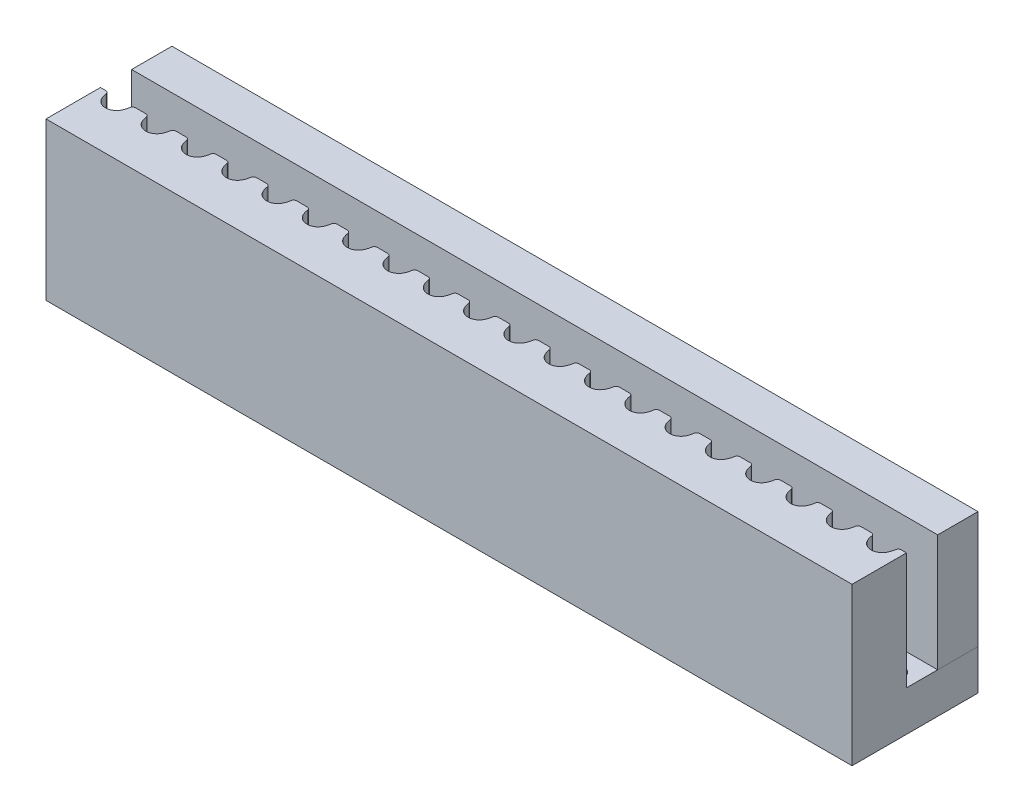
SolidWorks part; units mm, degrees
ref_plane "Front Plane" through (0, 0, 0) normal (0, 0, 1) x (1, 0, 0)
ref_plane "Top Plane" through (0, 0, 0) normal (0, 1, 0) x (1, 0, 0)
ref_plane "Right Plane" through (0, 0, 0) normal (1, 0, 0) x (0, 0, -1)
sketch "Sketch1" plane through (0, 0, 0) normal (0, 1, 0) x (1, 0, 0)
  line L0 (-20, 0.95) -> (20, 0.95) construction
  line L1 (0, -55) -> (0, 55) construction
  line L2 (-55, 0) -> (55, 0) construction
  line L3 (-20, 0.32) -> (20, 0.32)
  line L4 (-20, -0.43) -> (20, -0.43) construction
  line L5 (-19, 1.863) -> (-19, -1.7327) construction
  line L6 (-18.6, 1.863) -> (-18.6, -1.7327) construction
  line L7 (-20.453, 0.574) -> (20.5239, 0.574) construction
  line L8 (-19.4, 1.863) -> (-19.4, -1.7327) construction
  line L11 (-19.5915, 0.1896) -> (-17.5915, 0.1896) construction
  line L12 (20, 0.32) -> (20, -2.38)
  line L13 (20, -2.38) -> (-20, -2.38)
  line L14 (-20, -2.38) -> (-20, 0.32)
  line L17 (20, 1.87) -> (-20, 1.87)
  line L18 (20, 1.87) -> (20, 3.87)
  line L19 (20, 3.87) -> (-20, 3.87)
  line L20 (-20, 1.87) -> (-20, 3.87)
  circle A0 centre (-19, 0.125) radius 0.555
  arc A3 (-19.5915, 0.1896) -> (-19.7402, 0.32) centre (-19.7402, 0.17) ccw
  arc A4 (-18.2598, 0.32) -> (-18.4085, 0.1896) centre (-18.2598, 0.17) ccw
  arc A5 (-19.5915, 0.1896) -> (-19.4989, -0.1182) centre (-18.6, 0.32) ccw
  arc A6 (-18.5011, -0.1182) -> (-18.4085, 0.1896) centre (-19.4, 0.32) ccw
  arc A7 (-17.5915, 0.1896) -> (-17.7402, 0.32) centre (-17.7402, 0.17) ccw
  arc A8 (-17.5915, 0.1896) -> (-17.4989, -0.1182) centre (-16.6, 0.32) ccw
  circle A9 centre (-17, 0.125) radius 0.555
  arc A10 (-16.2598, 0.32) -> (-16.4085, 0.1896) centre (-16.2598, 0.17) ccw
  arc A11 (-16.5011, -0.1182) -> (-16.4085, 0.1896) centre (-17.4, 0.32) ccw
  arc A12 (-15.5915, 0.1896) -> (-15.7402, 0.32) centre (-15.7402, 0.17) ccw
  arc A13 (-15.5915, 0.1896) -> (-15.4989, -0.1182) centre (-14.6, 0.32) ccw
  circle A14 centre (-15, 0.125) radius 0.555
  arc A15 (-14.2598, 0.32) -> (-14.4085, 0.1896) centre (-14.2598, 0.17) ccw
  arc A16 (-14.5011, -0.1182) -> (-14.4085, 0.1896) centre (-15.4, 0.32) ccw
  arc A17 (-13.5915, 0.1896) -> (-13.7402, 0.32) centre (-13.7402, 0.17) ccw
  arc A18 (-13.5915, 0.1896) -> (-13.4989, -0.1182) centre (-12.6, 0.32) ccw
  circle A19 centre (-13, 0.125) radius 0.555
  arc A20 (-12.2598, 0.32) -> (-12.4085, 0.1896) centre (-12.2598, 0.17) ccw
  arc A21 (-12.5011, -0.1182) -> (-12.4085, 0.1896) centre (-13.4, 0.32) ccw
  arc A22 (-11.5915, 0.1896) -> (-11.7402, 0.32) centre (-11.7402, 0.17) ccw
  arc A23 (-11.5915, 0.1896) -> (-11.4989, -0.1182) centre (-10.6, 0.32) ccw
  circle A24 centre (-11, 0.125) radius 0.555
  arc A25 (-10.2598, 0.32) -> (-10.4085, 0.1896) centre (-10.2598, 0.17) ccw
  arc A26 (-10.5011, -0.1182) -> (-10.4085, 0.1896) centre (-11.4, 0.32) ccw
  arc A27 (-9.5915, 0.1896) -> (-9.7402, 0.32) centre (-9.7402, 0.17) ccw
  arc A28 (-9.5915, 0.1896) -> (-9.4989, -0.1182) centre (-8.6, 0.32) ccw
  circle A29 centre (-9, 0.125) radius 0.555
  arc A30 (-8.2598, 0.32) -> (-8.4085, 0.1896) centre (-8.2598, 0.17) ccw
  arc A31 (-8.5011, -0.1182) -> (-8.4085, 0.1896) centre (-9.4, 0.32) ccw
  arc A32 (-7.5915, 0.1896) -> (-7.7402, 0.32) centre (-7.7402, 0.17) ccw
  arc A33 (-7.5915, 0.1896) -> (-7.4989, -0.1182) centre (-6.6, 0.32) ccw
  circle A34 centre (-7, 0.125) radius 0.555
  arc A35 (-6.2598, 0.32) -> (-6.4085, 0.1896) centre (-6.2598, 0.17) ccw
  arc A36 (-6.5011, -0.1182) -> (-6.4085, 0.1896) centre (-7.4, 0.32) ccw
  arc A37 (-5.5915, 0.1896) -> (-5.7402, 0.32) centre (-5.7402, 0.17) ccw
  arc A38 (-5.5915, 0.1896) -> (-5.4989, -0.1182) centre (-4.6, 0.32) ccw
  circle A39 centre (-5, 0.125) radius 0.555
  arc A40 (-4.2598, 0.32) -> (-4.4085, 0.1896) centre (-4.2598, 0.17) ccw
  arc A41 (-4.5011, -0.1182) -> (-4.4085, 0.1896) centre (-5.4, 0.32) ccw
  arc A42 (-3.5915, 0.1896) -> (-3.7402, 0.32) centre (-3.7402, 0.17) ccw
  arc A43 (-3.5915, 0.1896) -> (-3.4989, -0.1182) centre (-2.6, 0.32) ccw
  circle A44 centre (-3, 0.125) radius 0.555
  arc A45 (-2.2598, 0.32) -> (-2.4085, 0.1896) centre (-2.2598, 0.17) ccw
  arc A46 (-2.5011, -0.1182) -> (-2.4085, 0.1896) centre (-3.4, 0.32) ccw
  arc A47 (-1.5915, 0.1896) -> (-1.7402, 0.32) centre (-1.7402, 0.17) ccw
  arc A48 (-1.5915, 0.1896) -> (-1.4989, -0.1182) centre (-0.6, 0.32) ccw
  circle A49 centre (-1, 0.125) radius 0.555
  arc A50 (-0.2598, 0.32) -> (-0.4085, 0.1896) centre (-0.2598, 0.17) ccw
  arc A51 (-0.5011, -0.1182) -> (-0.4085, 0.1896) centre (-1.4, 0.32) ccw
  arc A52 (0.4085, 0.1896) -> (0.2598, 0.32) centre (0.2598, 0.17) ccw
  arc A53 (0.4085, 0.1896) -> (0.5011, -0.1182) centre (1.4, 0.32) ccw
  circle A54 centre (1, 0.125) radius 0.555
  arc A55 (1.7402, 0.32) -> (1.5915, 0.1896) centre (1.7402, 0.17) ccw
  arc A56 (1.4989, -0.1182) -> (1.5915, 0.1896) centre (0.6, 0.32) ccw
  arc A57 (2.4085, 0.1896) -> (2.2598, 0.32) centre (2.2598, 0.17) ccw
  arc A58 (2.4085, 0.1896) -> (2.5011, -0.1182) centre (3.4, 0.32) ccw
  circle A59 centre (3, 0.125) radius 0.555
  arc A60 (3.7402, 0.32) -> (3.5915, 0.1896) centre (3.7402, 0.17) ccw
  arc A61 (3.4989, -0.1182) -> (3.5915, 0.1896) centre (2.6, 0.32) ccw
  arc A62 (4.4085, 0.1896) -> (4.2598, 0.32) centre (4.2598, 0.17) ccw
  arc A63 (4.4085, 0.1896) -> (4.5011, -0.1182) centre (5.4, 0.32) ccw
  circle A64 centre (5, 0.125) radius 0.555
  arc A65 (5.7402, 0.32) -> (5.5915, 0.1896) centre (5.7402, 0.17) ccw
  arc A66 (5.4989, -0.1182) -> (5.5915, 0.1896) centre (4.6, 0.32) ccw
  arc A67 (6.4085, 0.1896) -> (6.2598, 0.32) centre (6.2598, 0.17) ccw
  arc A68 (6.4085, 0.1896) -> (6.5011, -0.1182) centre (7.4, 0.32) ccw
  circle A69 centre (7, 0.125) radius 0.555
  arc A70 (7.7402, 0.32) -> (7.5915, 0.1896) centre (7.7402, 0.17) ccw
  arc A71 (7.4989, -0.1182) -> (7.5915, 0.1896) centre (6.6, 0.32) ccw
  arc A72 (8.4085, 0.1896) -> (8.2598, 0.32) centre (8.2598, 0.17) ccw
  arc A73 (8.4085, 0.1896) -> (8.5011, -0.1182) centre (9.4, 0.32) ccw
  circle A74 centre (9, 0.125) radius 0.555
  arc A75 (9.7402, 0.32) -> (9.5915, 0.1896) centre (9.7402, 0.17) ccw
  arc A76 (9.4989, -0.1182) -> (9.5915, 0.1896) centre (8.6, 0.32) ccw
  arc A77 (10.4085, 0.1896) -> (10.2598, 0.32) centre (10.2598, 0.17) ccw
  arc A78 (10.4085, 0.1896) -> (10.5011, -0.1182) centre (11.4, 0.32) ccw
  circle A79 centre (11, 0.125) radius 0.555
  arc A80 (11.7402, 0.32) -> (11.5915, 0.1896) centre (11.7402, 0.17) ccw
  arc A81 (11.4989, -0.1182) -> (11.5915, 0.1896) centre (10.6, 0.32) ccw
  arc A82 (12.4085, 0.1896) -> (12.2598, 0.32) centre (12.2598, 0.17) ccw
  arc A83 (12.4085, 0.1896) -> (12.5011, -0.1182) centre (13.4, 0.32) ccw
  circle A84 centre (13, 0.125) radius 0.555
  arc A85 (13.7402, 0.32) -> (13.5915, 0.1896) centre (13.7402, 0.17) ccw
  arc A86 (13.4989, -0.1182) -> (13.5915, 0.1896) centre (12.6, 0.32) ccw
  arc A87 (14.4085, 0.1896) -> (14.2598, 0.32) centre (14.2598, 0.17) ccw
  arc A88 (14.4085, 0.1896) -> (14.5011, -0.1182) centre (15.4, 0.32) ccw
  circle A89 centre (15, 0.125) radius 0.555
  arc A90 (15.7402, 0.32) -> (15.5915, 0.1896) centre (15.7402, 0.17) ccw
  arc A91 (15.4989, -0.1182) -> (15.5915, 0.1896) centre (14.6, 0.32) ccw
  arc A92 (16.4085, 0.1896) -> (16.2598, 0.32) centre (16.2598, 0.17) ccw
  arc A93 (16.4085, 0.1896) -> (16.5011, -0.1182) centre (17.4, 0.32) ccw
  circle A94 centre (17, 0.125) radius 0.555
  arc A95 (17.7402, 0.32) -> (17.5915, 0.1896) centre (17.7402, 0.17) ccw
  arc A96 (17.4989, -0.1182) -> (17.5915, 0.1896) centre (16.6, 0.32) ccw
  arc A97 (18.4085, 0.1896) -> (18.2598, 0.32) centre (18.2598, 0.17) ccw
  arc A98 (18.4085, 0.1896) -> (18.5011, -0.1182) centre (19.4, 0.32) ccw
  circle A99 centre (19, 0.125) radius 0.555
  arc A100 (19.7402, 0.32) -> (19.5915, 0.1896) centre (19.7402, 0.17) ccw
  arc A101 (19.4989, -0.1182) -> (19.5915, 0.1896) centre (18.6, 0.32) ccw
  point P2 (0, 0.95)
  dimension "D6" = 1.11
  dimension "D9" = 20
  dimension "D11" = 2
  dimension "D12" = 0.3
  dimension "D1" = 0.95
  dimension "D2" = 40
  dimension "D3" = 0.63
  dimension "D4" = 1.38
  dimension "D5" = 1
  dimension "D7" = 0.4
  dimension "D8" = 0.254
  dimension "D10" = 0.4
  dimension "D13" = 2.3
  dimension "D14" = 2
  dimension "D15" = 2.7
extrude "Boss-Extrude1" add sketch "Sketch1" along normal blind 5.8
sketch "Sketch2" plane through (0, 0, 0) normal (0, -1, 0) x (1, 0, 0)
  line L5 (-20, -1.87) -> (-20, -3.87) construction
  line L6 (-20, -3.87) -> (20, -3.87)
  line L7 (-17, -0.67) -> (-15, -0.67) construction
  line L8 (-17, -0.67) -> (-19, -0.67) construction
  line L9 (-20, -3.87) -> (-20, 2.38)
  line L10 (-20, 2.38) -> (20, 2.38)
  line L11 (20, -3.87) -> (20, 2.38)
  circle A0 centre (-17, -0.67) radius 0.5
  circle A1 centre (-15, -0.67) radius 0.5
  circle A2 centre (-13, -0.67) radius 0.5
  circle A3 centre (-11, -0.67) radius 0.5
  circle A4 centre (-9, -0.67) radius 0.5
  circle A5 centre (-7, -0.67) radius 0.5
  circle A6 centre (-5, -0.67) radius 0.5
  circle A7 centre (-3, -0.67) radius 0.5
  circle A8 centre (-1, -0.67) radius 0.5
  circle A9 centre (1, -0.67) radius 0.5
  circle A10 centre (3, -0.67) radius 0.5
  circle A11 centre (5, -0.67) radius 0.5
  circle A12 centre (7, -0.67) radius 0.5
  circle A13 centre (9, -0.67) radius 0.5
  circle A14 centre (11, -0.67) radius 0.5
  circle A15 centre (13, -0.67) radius 0.5
  circle A16 centre (15, -0.67) radius 0.5
  circle A17 centre (17, -0.67) radius 0.5
  circle A18 centre (19, -0.67) radius 0.5
  circle A20 centre (-19, -0.67) radius 0.5
  arc A21 (-16.5011, 0.1182) -> (-17.4989, 0.1182) centre (-17, -0.125) ccw construction
  circle A22 centre (21, -0.67) radius 0.5 [skipped]
  point P14 (-17, 0.43)
  dimension "D1" = 1
  dimension "D2" = 1.1
  dimension "D4" = 2
  dimension "D6" = 2
  dimension "D3" = 20
  dimension "D5" = 2
extrude "Boss-Extrude2" add sketch "Sketch2" along normal blind 2
